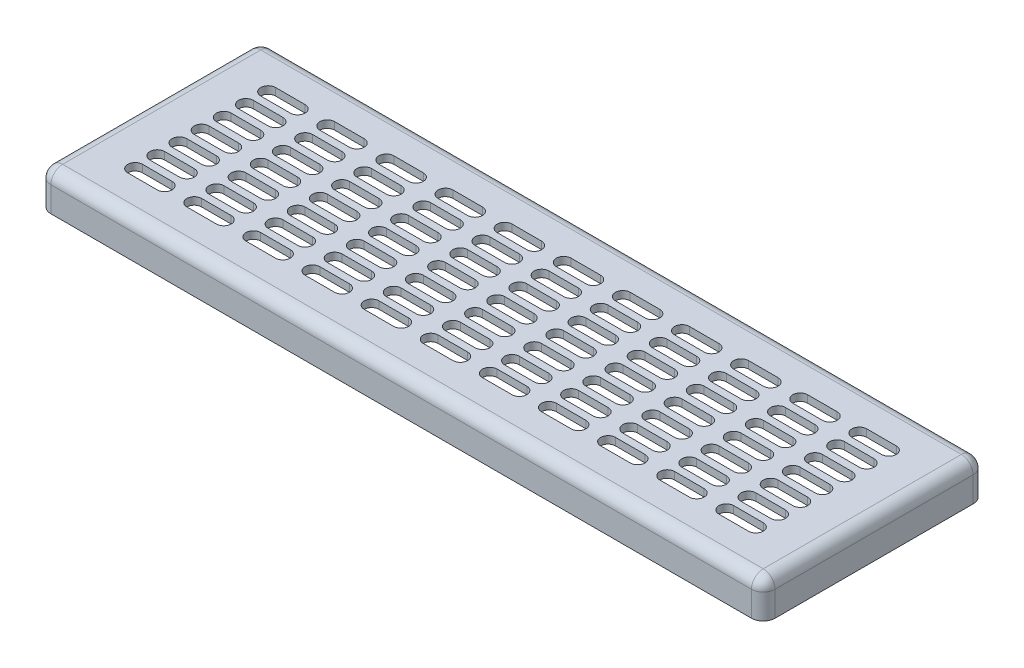
SolidWorks part; units mm, degrees
material "Cast Alloy Steel"
ref_plane "Front Plane" through (0, 0, 0) normal (0, 0, 1) x (1, 0, 0)
ref_plane "Top Plane" through (0, 0, 0) normal (0, 1, 0) x (1, 0, 0)
ref_plane "Right Plane" through (0, 0, 0) normal (1, 0, 0) x (0, 0, -1)
sketch "Sketch1" plane through (0, 0, 0) normal (0, 1, 0) x (1, 0, 0)
  line L1 (-245, -75) -> (245, -75)
  line L2 (-245, -75) -> (-245, 75)
  line L3 (-245, 75) -> (245, 75)
  line L4 (245, -75) -> (245, 75)
  line L5 (-245, -75) -> (245, 75) construction
  line L6 (-245, 75) -> (245, -75) construction
  line L9 (-285.6989, 45) -> (-35.2606, 45) construction
  line L10 (-200, 148.4214) -> (-200, -111.7901) construction
  dimension "D1" = 490
  dimension "D2" = 150
extrude "Boss-Extrude1" add sketch "Sketch1" along normal blind 25
fillet "Fillet1" radius 8 8 edges at (245, 25, 0) (0, 25, -75) (-245, 25, 0) (245, 12.5, 75) (-245, 12.5, 75) (-245, 12.5, -75) (245, 12.5, -75) (0, 25, 75)
shell "Shell2" thickness 5
sketch "Sketch2" plane through (0, 25, 0) normal (0, 1, 0) x (1, 0, 0)
  line L0 (-210, 45) -> (-190, 45) construction
  line L1 (-210, 50) -> (-190, 50)
  line L2 (-210, 40) -> (-190, 40)
  line L3 (-237, 75) -> (237, 75) construction
  line L4 (-245, -67) -> (-245, 67) construction
  line L5 (-200, 59.2875) -> (-200, 25.1472) construction
  line L6 (-173.5019, 45) -> (-222.6246, 45) construction
  line L7 (-170, 45) -> (-150, 45) construction
  line L8 (-170, 50) -> (-150, 50)
  line L9 (-170, 40) -> (-150, 40)
  line L10 (-130, 45) -> (-110, 45) construction
  line L11 (-130, 50) -> (-110, 50)
  line L12 (-130, 40) -> (-110, 40)
  line L13 (-90, 45) -> (-70, 45) construction
  line L14 (-90, 50) -> (-70, 50)
  line L15 (-90, 40) -> (-70, 40)
  line L16 (-50, 45) -> (-30, 45) construction
  line L17 (-50, 50) -> (-30, 50)
  line L18 (-50, 40) -> (-30, 40)
  line L19 (-10, 45) -> (10, 45) construction
  line L20 (-10, 50) -> (10, 50)
  line L21 (-10, 40) -> (10, 40)
  line L22 (30, 45) -> (50, 45) construction
  line L23 (30, 50) -> (50, 50)
  line L24 (30, 40) -> (50, 40)
  line L25 (70, 45) -> (90, 45) construction
  line L26 (70, 50) -> (90, 50)
  line L27 (70, 40) -> (90, 40)
  line L28 (110, 45) -> (130, 45) construction
  line L29 (110, 50) -> (130, 50)
  line L30 (110, 40) -> (130, 40)
  line L31 (150, 45) -> (170, 45) construction
  line L32 (150, 50) -> (170, 50)
  line L33 (150, 40) -> (170, 40)
  line L34 (190, 45) -> (210, 45) construction
  line L35 (190, 50) -> (210, 50)
  line L36 (190, 40) -> (210, 40)
  line L37 (-170, 30) -> (-150, 30) construction
  line L38 (-170, 35) -> (-150, 35)
  line L39 (-170, 25) -> (-150, 25)
  line L40 (-130, 30) -> (-110, 30) construction
  line L41 (-130, 35) -> (-110, 35)
  line L42 (-130, 25) -> (-110, 25)
  line L43 (-90, 30) -> (-70, 30) construction
  line L44 (-90, 35) -> (-70, 35)
  line L45 (-90, 25) -> (-70, 25)
  line L46 (-50, 30) -> (-30, 30) construction
  line L47 (-50, 35) -> (-30, 35)
  line L48 (-50, 25) -> (-30, 25)
  line L49 (-10, 30) -> (10, 30) construction
  line L50 (-10, 35) -> (10, 35)
  line L51 (-10, 25) -> (10, 25)
  line L52 (30, 30) -> (50, 30) construction
  line L53 (30, 35) -> (50, 35)
  line L54 (30, 25) -> (50, 25)
  line L55 (70, 30) -> (90, 30) construction
  line L56 (70, 35) -> (90, 35)
  line L57 (70, 25) -> (90, 25)
  line L58 (110, 30) -> (130, 30) construction
  line L59 (110, 35) -> (130, 35)
  line L60 (110, 25) -> (130, 25)
  line L61 (150, 30) -> (170, 30) construction
  line L62 (150, 35) -> (170, 35)
  line L63 (150, 25) -> (170, 25)
  line L64 (190, 30) -> (210, 30) construction
  line L65 (190, 35) -> (210, 35)
  line L66 (190, 25) -> (210, 25)
  line L67 (-170, 15) -> (-150, 15) construction
  line L68 (-170, 20) -> (-150, 20)
  line L69 (-170, 10) -> (-150, 10)
  line L70 (-130, 15) -> (-110, 15) construction
  line L71 (-130, 20) -> (-110, 20)
  line L72 (-130, 10) -> (-110, 10)
  line L73 (-90, 15) -> (-70, 15) construction
  line L74 (-90, 20) -> (-70, 20)
  line L75 (-90, 10) -> (-70, 10)
  line L76 (-50, 15) -> (-30, 15) construction
  line L77 (-50, 20) -> (-30, 20)
  line L78 (-50, 10) -> (-30, 10)
  line L79 (-10, 15) -> (10, 15) construction
  line L80 (-10, 20) -> (10, 20)
  line L81 (-10, 10) -> (10, 10)
  line L82 (30, 15) -> (50, 15) construction
  line L83 (30, 20) -> (50, 20)
  line L84 (30, 10) -> (50, 10)
  line L85 (70, 15) -> (90, 15) construction
  line L86 (70, 20) -> (90, 20)
  line L87 (70, 10) -> (90, 10)
  line L88 (110, 15) -> (130, 15) construction
  line L89 (110, 20) -> (130, 20)
  line L90 (110, 10) -> (130, 10)
  line L91 (150, 15) -> (170, 15) construction
  line L92 (150, 20) -> (170, 20)
  line L93 (150, 10) -> (170, 10)
  line L94 (190, 15) -> (210, 15) construction
  line L95 (190, 20) -> (210, 20)
  line L96 (190, 10) -> (210, 10)
  line L97 (-170, 0) -> (-150, 0) construction
  line L98 (-170, 5) -> (-150, 5)
  line L99 (-170, -5) -> (-150, -5)
  line L100 (-130, 0) -> (-110, 0) construction
  line L101 (-130, 5) -> (-110, 5)
  line L102 (-130, -5) -> (-110, -5)
  line L103 (-90, 0) -> (-70, 0) construction
  line L104 (-90, 5) -> (-70, 5)
  line L105 (-90, -5) -> (-70, -5)
  line L106 (-50, 0) -> (-30, 0) construction
  line L107 (-50, 5) -> (-30, 5)
  line L108 (-50, -5) -> (-30, -5)
  line L109 (-10, 0) -> (10, 0) construction
  line L110 (-10, 5) -> (10, 5)
  line L111 (-10, -5) -> (10, -5)
  line L112 (30, 0) -> (50, 0) construction
  line L113 (30, 5) -> (50, 5)
  line L114 (30, -5) -> (50, -5)
  line L115 (70, 0) -> (90, 0) construction
  line L116 (70, 5) -> (90, 5)
  line L117 (70, -5) -> (90, -5)
  line L118 (110, 0) -> (130, 0) construction
  line L119 (110, 5) -> (130, 5)
  line L120 (110, -5) -> (130, -5)
  line L121 (150, 0) -> (170, 0) construction
  line L122 (150, 5) -> (170, 5)
  line L123 (150, -5) -> (170, -5)
  line L124 (190, 0) -> (210, 0) construction
  line L125 (190, 5) -> (210, 5)
  line L126 (190, -5) -> (210, -5)
  line L127 (-170, -15) -> (-150, -15) construction
  line L128 (-170, -10) -> (-150, -10)
  line L129 (-170, -20) -> (-150, -20)
  line L130 (-130, -15) -> (-110, -15) construction
  line L131 (-130, -10) -> (-110, -10)
  line L132 (-130, -20) -> (-110, -20)
  line L133 (-90, -15) -> (-70, -15) construction
  line L134 (-90, -10) -> (-70, -10)
  line L135 (-90, -20) -> (-70, -20)
  line L136 (-50, -15) -> (-30, -15) construction
  line L137 (-50, -10) -> (-30, -10)
  line L138 (-50, -20) -> (-30, -20)
  line L139 (-10, -15) -> (10, -15) construction
  line L140 (-10, -10) -> (10, -10)
  line L141 (-10, -20) -> (10, -20)
  line L142 (30, -15) -> (50, -15) construction
  line L143 (30, -10) -> (50, -10)
  line L144 (30, -20) -> (50, -20)
  line L145 (70, -15) -> (90, -15) construction
  line L146 (70, -10) -> (90, -10)
  line L147 (70, -20) -> (90, -20)
  line L148 (110, -15) -> (130, -15) construction
  line L149 (110, -10) -> (130, -10)
  line L150 (110, -20) -> (130, -20)
  line L151 (150, -15) -> (170, -15) construction
  line L152 (150, -10) -> (170, -10)
  line L153 (150, -20) -> (170, -20)
  line L154 (190, -15) -> (210, -15) construction
  line L155 (190, -10) -> (210, -10)
  line L156 (190, -20) -> (210, -20)
  line L157 (-170, -30) -> (-150, -30) construction
  line L158 (-170, -25) -> (-150, -25)
  line L159 (-170, -35) -> (-150, -35)
  line L160 (-130, -30) -> (-110, -30) construction
  line L161 (-130, -25) -> (-110, -25)
  line L162 (-130, -35) -> (-110, -35)
  line L163 (-90, -30) -> (-70, -30) construction
  line L164 (-90, -25) -> (-70, -25)
  line L165 (-90, -35) -> (-70, -35)
  line L166 (-50, -30) -> (-30, -30) construction
  line L167 (-50, -25) -> (-30, -25)
  line L168 (-50, -35) -> (-30, -35)
  line L169 (-10, -30) -> (10, -30) construction
  line L170 (-10, -25) -> (10, -25)
  line L171 (-10, -35) -> (10, -35)
  line L172 (30, -30) -> (50, -30) construction
  line L173 (30, -25) -> (50, -25)
  line L174 (30, -35) -> (50, -35)
  line L175 (70, -30) -> (90, -30) construction
  line L176 (70, -25) -> (90, -25)
  line L177 (70, -35) -> (90, -35)
  line L178 (110, -30) -> (130, -30) construction
  line L179 (110, -25) -> (130, -25)
  line L180 (110, -35) -> (130, -35)
  line L181 (150, -30) -> (170, -30) construction
  line L182 (150, -25) -> (170, -25)
  line L183 (150, -35) -> (170, -35)
  line L184 (190, -30) -> (210, -30) construction
  line L185 (190, -25) -> (210, -25)
  line L186 (190, -35) -> (210, -35)
  line L187 (-170, -45) -> (-150, -45) construction
  line L188 (-170, -40) -> (-150, -40)
  line L189 (-170, -50) -> (-150, -50)
  line L190 (-130, -45) -> (-110, -45) construction
  line L191 (-130, -40) -> (-110, -40)
  line L192 (-130, -50) -> (-110, -50)
  line L193 (-90, -45) -> (-70, -45) construction
  line L194 (-90, -40) -> (-70, -40)
  line L195 (-90, -50) -> (-70, -50)
  line L196 (-50, -45) -> (-30, -45) construction
  line L197 (-50, -40) -> (-30, -40)
  line L198 (-50, -50) -> (-30, -50)
  line L199 (-10, -45) -> (10, -45) construction
  line L200 (-10, -40) -> (10, -40)
  line L201 (-10, -50) -> (10, -50)
  line L202 (30, -45) -> (50, -45) construction
  line L203 (30, -40) -> (50, -40)
  line L204 (30, -50) -> (50, -50)
  line L205 (70, -45) -> (90, -45) construction
  line L206 (70, -40) -> (90, -40)
  line L207 (70, -50) -> (90, -50)
  line L208 (110, -45) -> (130, -45) construction
  line L209 (110, -40) -> (130, -40)
  line L210 (110, -50) -> (130, -50)
  line L211 (150, -45) -> (170, -45) construction
  line L212 (150, -40) -> (170, -40)
  line L213 (150, -50) -> (170, -50)
  line L214 (190, -45) -> (210, -45) construction
  line L215 (190, -40) -> (210, -40)
  line L216 (190, -50) -> (210, -50)
  line L217 (-210, 30) -> (-190, 30) construction
  line L218 (-210, 35) -> (-190, 35)
  line L219 (-210, 25) -> (-190, 25)
  line L220 (-210, 15) -> (-190, 15) construction
  line L221 (-210, 20) -> (-190, 20)
  line L222 (-210, 10) -> (-190, 10)
  line L223 (-210, 0) -> (-190, 0) construction
  line L224 (-210, 5) -> (-190, 5)
  line L225 (-210, -5) -> (-190, -5)
  line L226 (-210, -15) -> (-190, -15) construction
  line L227 (-210, -10) -> (-190, -10)
  line L228 (-210, -20) -> (-190, -20)
  line L229 (-210, -30) -> (-190, -30) construction
  line L230 (-210, -25) -> (-190, -25)
  line L231 (-210, -35) -> (-190, -35)
  line L232 (-210, -45) -> (-190, -45) construction
  line L233 (-210, -40) -> (-190, -40)
  line L234 (-210, -50) -> (-190, -50)
  arc A0 (-210, 50) -> (-210, 40) centre (-210, 45) ccw
  arc A1 (-190, 40) -> (-190, 50) centre (-190, 45) ccw
  arc A2 (-170, 50) -> (-170, 40) centre (-170, 45) ccw
  arc A3 (-150, 40) -> (-150, 50) centre (-150, 45) ccw
  arc A4 (-130, 50) -> (-130, 40) centre (-130, 45) ccw
  arc A5 (-110, 40) -> (-110, 50) centre (-110, 45) ccw
  arc A6 (-90, 50) -> (-90, 40) centre (-90, 45) ccw
  arc A7 (-70, 40) -> (-70, 50) centre (-70, 45) ccw
  arc A8 (-50, 50) -> (-50, 40) centre (-50, 45) ccw
  arc A9 (-30, 40) -> (-30, 50) centre (-30, 45) ccw
  arc A10 (-10, 50) -> (-10, 40) centre (-10, 45) ccw
  arc A11 (10, 40) -> (10, 50) centre (10, 45) ccw
  arc A12 (30, 50) -> (30, 40) centre (30, 45) ccw
  arc A13 (50, 40) -> (50, 50) centre (50, 45) ccw
  arc A14 (70, 50) -> (70, 40) centre (70, 45) ccw
  arc A15 (90, 40) -> (90, 50) centre (90, 45) ccw
  arc A16 (110, 50) -> (110, 40) centre (110, 45) ccw
  arc A17 (130, 40) -> (130, 50) centre (130, 45) ccw
  arc A18 (150, 50) -> (150, 40) centre (150, 45) ccw
  arc A19 (170, 40) -> (170, 50) centre (170, 45) ccw
  arc A20 (190, 50) -> (190, 40) centre (190, 45) ccw
  arc A21 (210, 40) -> (210, 50) centre (210, 45) ccw
  arc A22 (-170, 35) -> (-170, 25) centre (-170, 30) ccw
  arc A23 (-150, 25) -> (-150, 35) centre (-150, 30) ccw
  arc A24 (-130, 35) -> (-130, 25) centre (-130, 30) ccw
  arc A25 (-110, 25) -> (-110, 35) centre (-110, 30) ccw
  arc A26 (-90, 35) -> (-90, 25) centre (-90, 30) ccw
  arc A27 (-70, 25) -> (-70, 35) centre (-70, 30) ccw
  arc A28 (-50, 35) -> (-50, 25) centre (-50, 30) ccw
  arc A29 (-30, 25) -> (-30, 35) centre (-30, 30) ccw
  arc A30 (-10, 35) -> (-10, 25) centre (-10, 30) ccw
  arc A31 (10, 25) -> (10, 35) centre (10, 30) ccw
  arc A32 (30, 35) -> (30, 25) centre (30, 30) ccw
  arc A33 (50, 25) -> (50, 35) centre (50, 30) ccw
  arc A34 (70, 35) -> (70, 25) centre (70, 30) ccw
  arc A35 (90, 25) -> (90, 35) centre (90, 30) ccw
  arc A36 (110, 35) -> (110, 25) centre (110, 30) ccw
  arc A37 (130, 25) -> (130, 35) centre (130, 30) ccw
  arc A38 (150, 35) -> (150, 25) centre (150, 30) ccw
  arc A39 (170, 25) -> (170, 35) centre (170, 30) ccw
  arc A40 (190, 35) -> (190, 25) centre (190, 30) ccw
  arc A41 (210, 25) -> (210, 35) centre (210, 30) ccw
  arc A42 (-170, 20) -> (-170, 10) centre (-170, 15) ccw
  arc A43 (-150, 10) -> (-150, 20) centre (-150, 15) ccw
  arc A44 (-130, 20) -> (-130, 10) centre (-130, 15) ccw
  arc A45 (-110, 10) -> (-110, 20) centre (-110, 15) ccw
  arc A46 (-90, 20) -> (-90, 10) centre (-90, 15) ccw
  arc A47 (-70, 10) -> (-70, 20) centre (-70, 15) ccw
  arc A48 (-50, 20) -> (-50, 10) centre (-50, 15) ccw
  arc A49 (-30, 10) -> (-30, 20) centre (-30, 15) ccw
  arc A50 (-10, 20) -> (-10, 10) centre (-10, 15) ccw
  arc A51 (10, 10) -> (10, 20) centre (10, 15) ccw
  arc A52 (30, 20) -> (30, 10) centre (30, 15) ccw
  arc A53 (50, 10) -> (50, 20) centre (50, 15) ccw
  arc A54 (70, 20) -> (70, 10) centre (70, 15) ccw
  arc A55 (90, 10) -> (90, 20) centre (90, 15) ccw
  arc A56 (110, 20) -> (110, 10) centre (110, 15) ccw
  arc A57 (130, 10) -> (130, 20) centre (130, 15) ccw
  arc A58 (150, 20) -> (150, 10) centre (150, 15) ccw
  arc A59 (170, 10) -> (170, 20) centre (170, 15) ccw
  arc A60 (190, 20) -> (190, 10) centre (190, 15) ccw
  arc A61 (210, 10) -> (210, 20) centre (210, 15) ccw
  arc A62 (-170, 5) -> (-170, -5) centre (-170, 0) ccw
  arc A63 (-150, -5) -> (-150, 5) centre (-150, 0) ccw
  arc A64 (-130, 5) -> (-130, -5) centre (-130, 0) ccw
  arc A65 (-110, -5) -> (-110, 5) centre (-110, 0) ccw
  arc A66 (-90, 5) -> (-90, -5) centre (-90, 0) ccw
  arc A67 (-70, -5) -> (-70, 5) centre (-70, 0) ccw
  arc A68 (-50, 5) -> (-50, -5) centre (-50, 0) ccw
  arc A69 (-30, -5) -> (-30, 5) centre (-30, 0) ccw
  arc A70 (-10, 5) -> (-10, -5) centre (-10, 0) ccw
  arc A71 (10, -5) -> (10, 5) centre (10, 0) ccw
  arc A72 (30, 5) -> (30, -5) centre (30, 0) ccw
  arc A73 (50, -5) -> (50, 5) centre (50, 0) ccw
  arc A74 (70, 5) -> (70, -5) centre (70, 0) ccw
  arc A75 (90, -5) -> (90, 5) centre (90, 0) ccw
  arc A76 (110, 5) -> (110, -5) centre (110, 0) ccw
  arc A77 (130, -5) -> (130, 5) centre (130, 0) ccw
  arc A78 (150, 5) -> (150, -5) centre (150, 0) ccw
  arc A79 (170, -5) -> (170, 5) centre (170, 0) ccw
  arc A80 (190, 5) -> (190, -5) centre (190, 0) ccw
  arc A81 (210, -5) -> (210, 5) centre (210, 0) ccw
  arc A82 (-170, -10) -> (-170, -20) centre (-170, -15) ccw
  arc A83 (-150, -20) -> (-150, -10) centre (-150, -15) ccw
  arc A84 (-130, -10) -> (-130, -20) centre (-130, -15) ccw
  arc A85 (-110, -20) -> (-110, -10) centre (-110, -15) ccw
  arc A86 (-90, -10) -> (-90, -20) centre (-90, -15) ccw
  arc A87 (-70, -20) -> (-70, -10) centre (-70, -15) ccw
  arc A88 (-50, -10) -> (-50, -20) centre (-50, -15) ccw
  arc A89 (-30, -20) -> (-30, -10) centre (-30, -15) ccw
  arc A90 (-10, -10) -> (-10, -20) centre (-10, -15) ccw
  arc A91 (10, -20) -> (10, -10) centre (10, -15) ccw
  arc A92 (30, -10) -> (30, -20) centre (30, -15) ccw
  arc A93 (50, -20) -> (50, -10) centre (50, -15) ccw
  arc A94 (70, -10) -> (70, -20) centre (70, -15) ccw
  arc A95 (90, -20) -> (90, -10) centre (90, -15) ccw
  arc A96 (110, -10) -> (110, -20) centre (110, -15) ccw
  arc A97 (130, -20) -> (130, -10) centre (130, -15) ccw
  arc A98 (150, -10) -> (150, -20) centre (150, -15) ccw
  arc A99 (170, -20) -> (170, -10) centre (170, -15) ccw
  arc A100 (190, -10) -> (190, -20) centre (190, -15) ccw
  arc A101 (210, -20) -> (210, -10) centre (210, -15) ccw
  arc A102 (-170, -25) -> (-170, -35) centre (-170, -30) ccw
  arc A103 (-150, -35) -> (-150, -25) centre (-150, -30) ccw
  arc A104 (-130, -25) -> (-130, -35) centre (-130, -30) ccw
  arc A105 (-110, -35) -> (-110, -25) centre (-110, -30) ccw
  arc A106 (-90, -25) -> (-90, -35) centre (-90, -30) ccw
  arc A107 (-70, -35) -> (-70, -25) centre (-70, -30) ccw
  arc A108 (-50, -25) -> (-50, -35) centre (-50, -30) ccw
  arc A109 (-30, -35) -> (-30, -25) centre (-30, -30) ccw
  arc A110 (-10, -25) -> (-10, -35) centre (-10, -30) ccw
  arc A111 (10, -35) -> (10, -25) centre (10, -30) ccw
  arc A112 (30, -25) -> (30, -35) centre (30, -30) ccw
  arc A113 (50, -35) -> (50, -25) centre (50, -30) ccw
  arc A114 (70, -25) -> (70, -35) centre (70, -30) ccw
  arc A115 (90, -35) -> (90, -25) centre (90, -30) ccw
  arc A116 (110, -25) -> (110, -35) centre (110, -30) ccw
  arc A117 (130, -35) -> (130, -25) centre (130, -30) ccw
  arc A118 (150, -25) -> (150, -35) centre (150, -30) ccw
  arc A119 (170, -35) -> (170, -25) centre (170, -30) ccw
  arc A120 (190, -25) -> (190, -35) centre (190, -30) ccw
  arc A121 (210, -35) -> (210, -25) centre (210, -30) ccw
  arc A122 (-170, -40) -> (-170, -50) centre (-170, -45) ccw
  arc A123 (-150, -50) -> (-150, -40) centre (-150, -45) ccw
  arc A124 (-130, -40) -> (-130, -50) centre (-130, -45) ccw
  arc A125 (-110, -50) -> (-110, -40) centre (-110, -45) ccw
  arc A126 (-90, -40) -> (-90, -50) centre (-90, -45) ccw
  arc A127 (-70, -50) -> (-70, -40) centre (-70, -45) ccw
  arc A128 (-50, -40) -> (-50, -50) centre (-50, -45) ccw
  arc A129 (-30, -50) -> (-30, -40) centre (-30, -45) ccw
  arc A130 (-10, -40) -> (-10, -50) centre (-10, -45) ccw
  arc A131 (10, -50) -> (10, -40) centre (10, -45) ccw
  arc A132 (30, -40) -> (30, -50) centre (30, -45) ccw
  arc A133 (50, -50) -> (50, -40) centre (50, -45) ccw
  arc A134 (70, -40) -> (70, -50) centre (70, -45) ccw
  arc A135 (90, -50) -> (90, -40) centre (90, -45) ccw
  arc A136 (110, -40) -> (110, -50) centre (110, -45) ccw
  arc A137 (130, -50) -> (130, -40) centre (130, -45) ccw
  arc A138 (150, -40) -> (150, -50) centre (150, -45) ccw
  arc A139 (170, -50) -> (170, -40) centre (170, -45) ccw
  arc A140 (190, -40) -> (190, -50) centre (190, -45) ccw
  arc A141 (210, -50) -> (210, -40) centre (210, -45) ccw
  arc A142 (-210, 35) -> (-210, 25) centre (-210, 30) ccw
  arc A143 (-190, 25) -> (-190, 35) centre (-190, 30) ccw
  arc A144 (-210, 20) -> (-210, 10) centre (-210, 15) ccw
  arc A145 (-190, 10) -> (-190, 20) centre (-190, 15) ccw
  arc A146 (-210, 5) -> (-210, -5) centre (-210, 0) ccw
  arc A147 (-190, -5) -> (-190, 5) centre (-190, 0) ccw
  arc A148 (-210, -10) -> (-210, -20) centre (-210, -15) ccw
  arc A149 (-190, -20) -> (-190, -10) centre (-190, -15) ccw
  arc A150 (-210, -25) -> (-210, -35) centre (-210, -30) ccw
  arc A151 (-190, -35) -> (-190, -25) centre (-190, -30) ccw
  arc A152 (-210, -40) -> (-210, -50) centre (-210, -45) ccw
  arc A153 (-190, -50) -> (-190, -40) centre (-190, -45) ccw
  point P2 (-200, 45)
  point P20 (-160, 45)
  point P27 (-120, 45)
  point P34 (-80, 45)
  point P41 (-40, 45)
  point P48 (0, 45)
  point P55 (40, 45)
  point P62 (80, 45)
  point P69 (120, 45)
  point P76 (160, 45)
  point P83 (200, 45)
  point P90 (-160, 30)
  point P97 (-120, 30)
  point P104 (-80, 30)
  point P111 (-40, 30)
  point P118 (0, 30)
  point P125 (40, 30)
  point P132 (80, 30)
  point P139 (120, 30)
  point P146 (160, 30)
  point P153 (200, 30)
  point P160 (-160, 15)
  point P167 (-120, 15)
  point P174 (-80, 15)
  point P181 (-40, 15)
  point P188 (0, 15)
  point P195 (40, 15)
  point P202 (80, 15)
  point P209 (120, 15)
  point P216 (160, 15)
  point P223 (200, 15)
  point P230 (-160, 0)
  point P237 (-120, 0)
  point P244 (-80, 0)
  point P251 (-40, 0)
  point P258 (0, 0)
  point P265 (40, 0)
  point P272 (80, 0)
  point P279 (120, 0)
  point P286 (160, 0)
  point P293 (200, 0)
  point P300 (-160, -15)
  point P307 (-120, -15)
  point P314 (-80, -15)
  point P321 (-40, -15)
  point P328 (0, -15)
  point P335 (40, -15)
  point P342 (80, -15)
  point P349 (120, -15)
  point P356 (160, -15)
  point P363 (200, -15)
  point P370 (-160, -30)
  point P377 (-120, -30)
  point P384 (-80, -30)
  point P391 (-40, -30)
  point P398 (0, -30)
  point P405 (40, -30)
  point P412 (80, -30)
  point P419 (120, -30)
  point P426 (160, -30)
  point P433 (200, -30)
  point P440 (-160, -45)
  point P447 (-120, -45)
  point P454 (-80, -45)
  point P461 (-40, -45)
  point P468 (0, -45)
  point P475 (40, -45)
  point P482 (80, -45)
  point P489 (120, -45)
  point P496 (160, -45)
  point P503 (200, -45)
  point P510 (-200, 30)
  point P517 (-200, 15)
  point P524 (-200, 0)
  point P531 (-200, -15)
  point P538 (-200, -30)
  point P545 (-200, -45)
  dimension "D3" = 5
  dimension "D1" = 30
  dimension "D2" = 35
  dimension "D4" = 20
extrude "Cut-Extrude1" cut sketch "Sketch2" against normal through all
